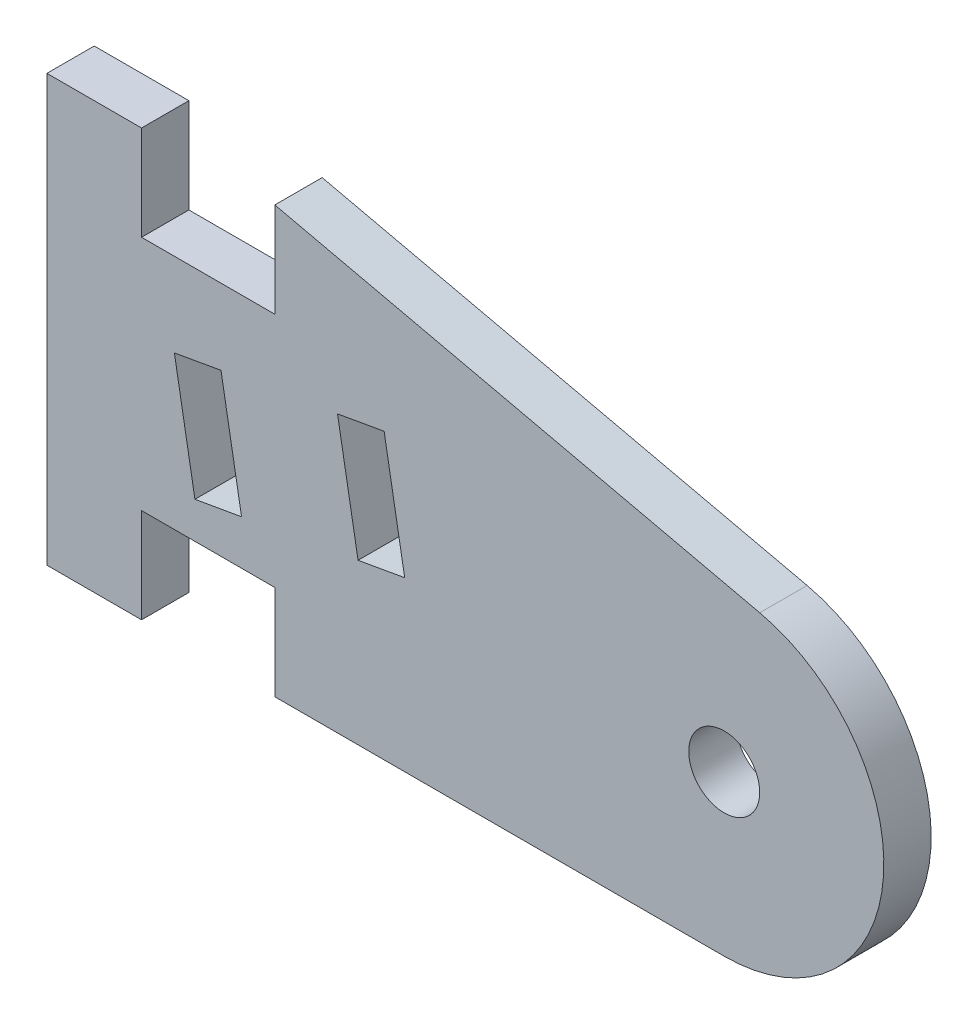
SolidWorks part; units mm, degrees
ref_plane "Front Plane" through (0, 0, 0) normal (0, 0, 1) x (1, 0, 0)
ref_plane "Top Plane" through (0, 0, 0) normal (0, 1, 0) x (1, 0, 0)
ref_plane "Right Plane" through (0, 0, 0) normal (1, 0, 0) x (0, 0, -1)
sketch "Sketch1" plane through (0, 0, 0) normal (0, 0, 1) x (1, 0, 0)
  line L0 (0, 0) -> (0, 18.0003)
  line L1 (9.6315, 0) -> (9.6315, 4)
  line L2 (9.6315, 4) -> (4, 4)
  line L3 (9.6315, 18.0003) -> (30.1232, 13.3208)
  line L4 (9.6315, 18.0003) -> (9.6315, 14.0003)
  line L5 (9.6315, 14.0003) -> (4, 14.0003)
  line L6 (0, 0) -> (4, 0)
  line L7 (4, 0) -> (4, 4)
  line L9 (14.2505, 12.0256) -> (12.2808, 11.6783)
  line L10 (7.3568, 10.81) -> (8.225, 5.886)
  line L11 (7.3568, 10.81) -> (5.3872, 10.4627)
  line L12 (4, 18.0003) -> (4, 14.0003)
  line L13 (0, 18.0003) -> (4, 18.0003)
  line L14 (5.3872, 10.4627) -> (6.2554, 5.5387)
  line L15 (6.2554, 5.5387) -> (8.225, 5.886)
  line L16 (12.2808, 11.6783) -> (13.1491, 6.7542)
  line L17 (13.1491, 6.7542) -> (15.1187, 7.1015)
  line L18 (14.2505, 12.0256) -> (15.1187, 7.1015)
  line L20 (9.6315, 0) -> (28.6215, 0)
  circle A0 centre (28.6215, 6.745) radius 12.12 construction
  arc A1 (28.6215, 0) -> (30.1232, 13.3208) centre (28.6215, 6.745) ccw
  circle A5 centre (28.6215, 6.745) radius 1.5
  dimension "D1" = 3
  dimension "D2" = 6.745
  dimension "D12" = 24.24
  dimension "D4" = 5.3872
  dimension "D5" = 6.2554
  dimension "D6" = 7.3568
  dimension "D7" = 12.2808
  dimension "D8" = 18.0003
  dimension "D9" = 5.6315
  dimension "D10" = 5.5387
  dimension "D11" = 5.886
  dimension "D13" = 9.6315
  dimension "ThumbLinkLengthMCP" = 18.99
extrude "Boss-Extrude1" add sketch "Sketch1" along normal blind 2
equation "\"ThumbLinkLengthMCP@Sketch1\"= \"HB@parametersSketch@prostheticParameters.SLDPRT\" * 0.211"
